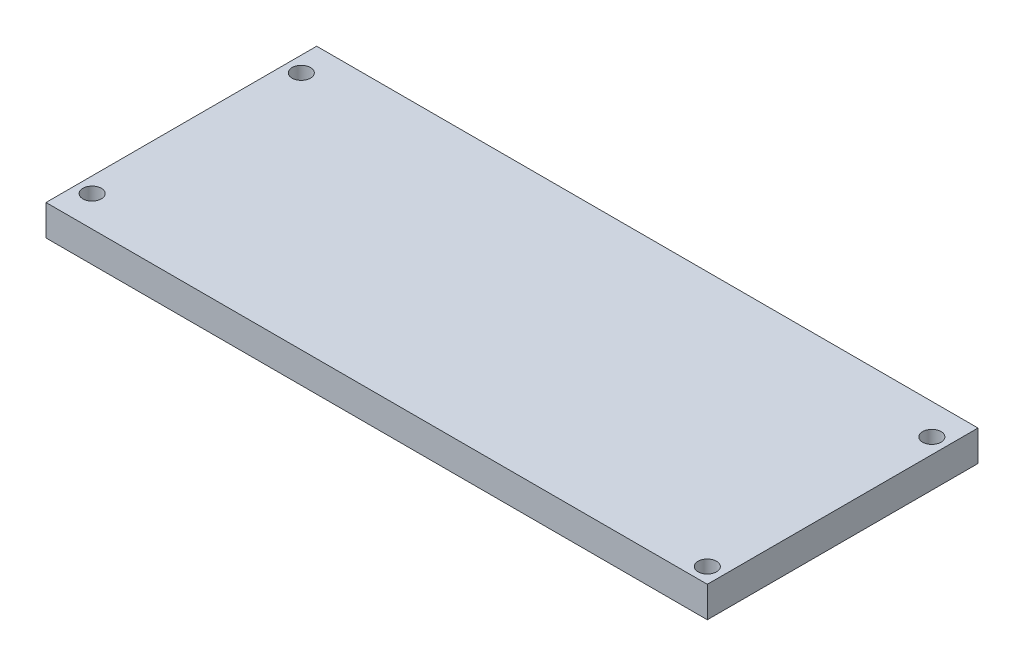
SolidWorks part; units mm, degrees
ref_plane "Front Plane" through (0, 0, 0) normal (0, 0, 1) x (1, 0, 0)
ref_plane "Top Plane" through (0, 0, 0) normal (0, 1, 0) x (1, 0, 0)
ref_plane "Right Plane" through (0, 0, 0) normal (1, 0, 0) x (0, 0, -1)
sketch "Sketch1" plane through (0, 0, 0) normal (0, 1, 0) x (1, 0, 0)
  line L1 (0, 88) -> (215, 88)
  line L2 (0, 88) -> (0, 0)
  line L3 (0, 0) -> (215, 0)
  line L4 (215, 88) -> (215, 0)
  circle A0 centre (5, 78) radius 3
  circle A1 centre (5, 10) radius 3
  circle A2 centre (210, 78) radius 3
  circle A3 centre (210, 5) radius 3
  point P12 (0, 0)
  point P13 (0, 0)
  point P14 (0, 0)
  point P15 (0, 0)
  point P16 (0, 0)
  point P17 (0, 0)
  point P18 (0, 0)
extrude "Boss-Extrude1" add sketch "Sketch1" along normal blind 10
